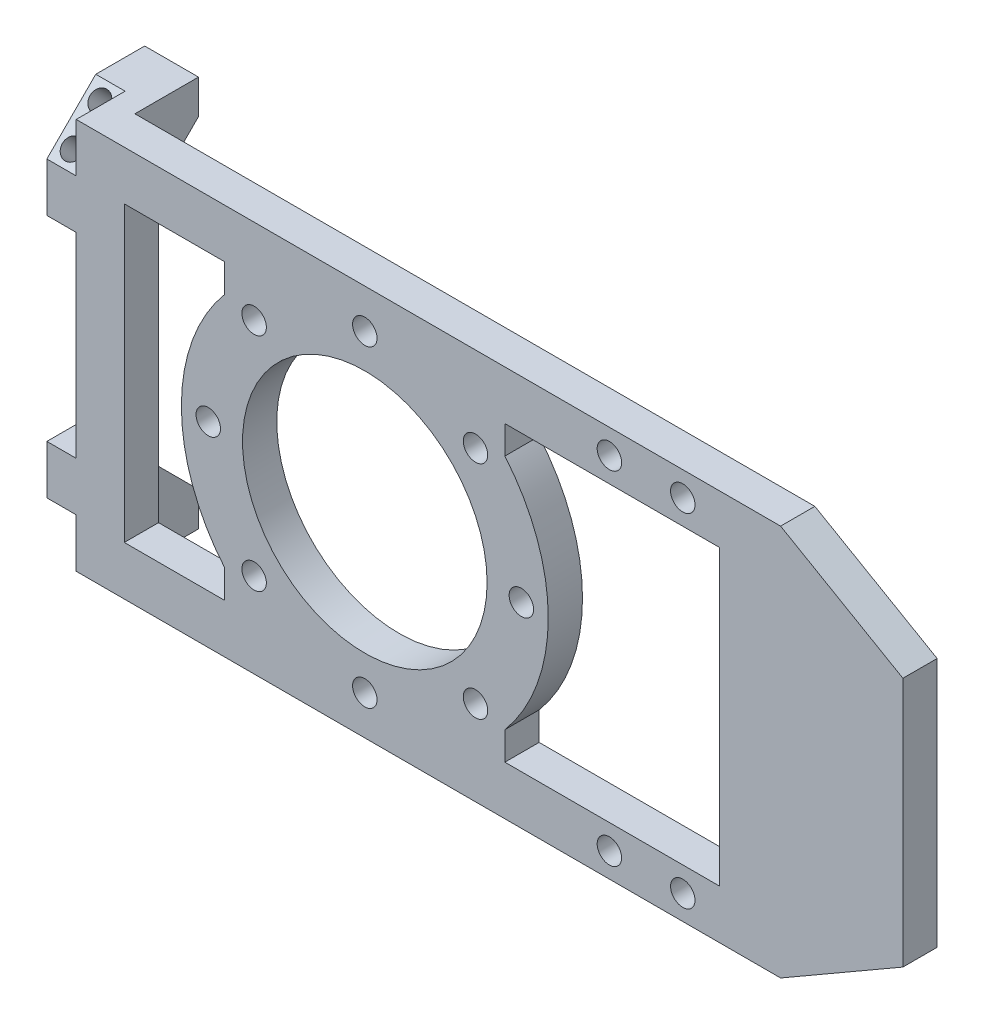
SolidWorks part; units mm, degrees
ref_plane "Front Plane" through (0, 0, 0) normal (0, 0, 1) x (1, 0, 0)
ref_plane "Top Plane" through (0, 0, 0) normal (0, 1, 0) x (1, 0, 0)
ref_plane "Right Plane" through (0, 0, 0) normal (1, 0, 0) x (0, 0, -1)
sketch "Sketch1" plane through (0, 0, 0) normal (0, 0, 1) x (1, 0, 0)
  line L1 (0, 0) -> (150, 0)
  line L2 (0, 0) -> (0, 80)
  line L3 (0, 80) -> (150, 80)
  line L4 (150, 0) -> (150, 80)
  dimension "D1" = 80
  dimension "D2" = 150
extrude "Boss-Extrude1" add sketch "Sketch1" along normal blind 7
sketch "Sketch2" plane through (0, 0, 7) normal (0, 0, 1) x (1, 0, 0)
  line L3 (0, 60) -> (6, 60)
  line L7 (0, 20) -> (6, 20)
  line L9 (0, 60) -> (6, 60)
  line L10 (0, 60) -> (0, 20)
  line L11 (0, 20) -> (6, 20)
  line L12 (6, 60) -> (6, 20)
  line M4 (0, 80) -> (0, 0)
extrude "Cut-Extrude2" cut sketch "Sketch2" against normal blind 7 contours L12 L3 L7 M4
sketch "Sketch3" plane through (0, 0, 7) normal (0, 0, 1) x (1, 0, 0)
  line L0 (150, 0) -> (150, 80) construction
  circle A0 centre (65, 40) radius 25
  dimension "D1" = 50
  dimension "D2" = 85
extrude "Cut-Extrude3" cut sketch "Sketch3" against normal blind 7
sketch "Sketch4" plane through (0, 0, 7) normal (0, 0, 1) x (1, 0, 0)
  line L0 (15.8284, 69.9752) -> (15.8284, 10.0248)
  line L1 (15.8284, 69.9752) -> (36.3588, 69.9752)
  line L3 (15.8284, 10.0248) -> (36.3588, 10.0248)
  line L5 (-2.1302, 69.9752) -> (42.4669, 10.0248) construction
  line L6 (-2.1302, 10.0248) -> (42.4669, 69.9752) construction
  line L7 (36.3588, 69.9752) -> (36.3588, 64.206)
  line L8 (36.3588, 15.794) -> (36.3588, 10.0248)
  arc A0 (36.3588, 64.206) -> (36.3588, 15.794) centre (65, 40) ccw
  point P3 (20.1684, 40)
  dimension "D1" = 75
extrude "Cut-Extrude5" cut sketch "Sketch4" against normal blind 7
sketch "Sketch5" plane through (0, 0, 7) normal (0, 0, 1) x (1, 0, 0)
  line L0 (93.6312, 69.9752) -> (93.6312, 64.2179)
  line L1 (93.6312, 69.9752) -> (137.5331, 69.9752)
  line L3 (93.6312, 10.0248) -> (137.5331, 10.0248)
  line L4 (137.5331, 69.9752) -> (137.5331, 10.0248)
  line L5 (93.6312, 15.7821) -> (93.6312, 10.0248)
  arc A0 (93.6312, 15.7821) -> (93.6312, 64.2179) centre (65, 40) ccw
extrude "Cut-Extrude6" cut sketch "Sketch5" against normal blind 7
sketch "Sketch6" plane through (0, 0, 7) normal (0, 0, 1) x (1, 0, 0)
  circle A0 centre (97, 40) radius 2.5
  circle A1 centre (65, 40) radius 25 construction
  circle A2 centre (87.6274, 17.3726) radius 2.5
  circle A3 centre (65, 8) radius 2.5
  circle A4 centre (42.3726, 17.3726) radius 2.5
  circle A5 centre (33, 40) radius 2.5
  circle A6 centre (42.3726, 62.6274) radius 2.5
  circle A7 centre (65, 72) radius 2.5
  circle A8 centre (87.6274, 62.6274) radius 2.5
  point P20 (65, 40)
  dimension "D1" = 5
  dimension "D2" = 32
  dimension "D3" = 8
extrude "Cut-Extrude7" cut sketch "Sketch6" against normal blind 7
sketch "Sketch8" plane through (0, 0, 0) normal (-1, 0, 0) x (0, 0, 1)
  line L0 (0, 60) -> (-20, 80)
  line L1 (-20, 80) -> (0, 80)
  line L2 (0, 80) -> (0, 60)
extrude "Boss-Extrude2" add sketch "Sketch8" against normal blind 6
sketch "Sketch9" plane through (0, 0, 0) normal (-1, 0, 0) x (0, 0, 1)
  line L0 (-13, 80) -> (-13, 73)
  line L1 (7, 80) -> (-20, 80) construction
  line L2 (-20, 80) -> (0, 60) construction
  line L3 (0, 60) -> (0, 20) construction
  line L4 (-13, 73) -> (-20, 80)
  line L5 (-20, 80) -> (-13, 80)
  dimension "D1" = 13
extrude "Cut-Extrude8" cut sketch "Sketch9" against normal blind 6
sketch "Sketch10" plane through (0, 0, 0) normal (0, 0, -1) x (-1, 0, 0)
  line L1 (-6, 20) -> (0, 20)
  line L2 (-6, 20) -> (-6, 0)
  line L3 (-6, 0) -> (0, 0)
  line L4 (0, 20) -> (0, 0)
extrude "Boss-Extrude3" add sketch "Sketch10" along normal blind 13
sketch "Sketch11" plane through (0, 0, 0) normal (-1, 0, 0) x (0, 0, 1)
  line L0 (0, 20) -> (-13, 7)
  line L1 (-13, 0) -> (-13, 20) construction
  line L2 (-13, 7) -> (-13, 20)
  line L3 (-13, 20) -> (0, 20)
extrude "Cut-Extrude9" cut sketch "Sketch11" against normal blind 13
sketch "Sketch12" plane through (0, 0, 7) normal (0, 0, 1) x (1, 0, 0)
  line L0 (150, 0) -> (150, 80) construction
  line L1 (150, 80) -> (0, 80) construction
  line L3 (150, 40) -> (139.1151, 40) construction
  circle A0 centre (130, 75) radius 2.5
  circle A1 centre (115, 75) radius 2.5
  circle A2 centre (130, 5) radius 2.5
  circle A3 centre (115, 5) radius 2.5
  dimension "D1" = 20
  dimension "D2" = 5
  dimension "D3" = 5
  dimension "D4" = 5
  dimension "D5" = 15
extrude "Cut-Extrude10" cut sketch "Sketch12" against normal blind 13
sketch "Sketch13" plane through (6, 0, 0) normal (1, 0, 0) x (0, 0, -1)
  line L0 (0, 60) -> (13, 73)
  line L1 (13, 73) -> (13, 80)
  line L2 (13, 80) -> (0, 80)
  line L3 (0, 80) -> (0, 60)
  line L4 (-7, 40) -> (-3.6324, 40) construction
  line L5 (-7, 0) -> (-7, 80) construction
  line L6 (13, 0) -> (0, 0)
  line L7 (13, 7) -> (13, 0)
  line L8 (0, 20) -> (13, 7)
  line L9 (0, 0) -> (0, 20)
extrude "Boss-Extrude5" add sketch "Sketch13" along normal blind 5
sketch "Sketch14" plane through (0, 30, 30) normal (0, -0.7071, -0.7071) x (1, 0, 0)
  line L0 (3, -55.6188) -> (3, -47.6188)
  circle A0 centre (3, -47.6188) radius 2
  circle A1 centre (3, -55.6188) radius 2
  point P3 (3, -51.6188)
  point P5 (0, 0)
  dimension "D2" = 4
  dimension "D3" = 4
  dimension "D1" = 8
extrude "Cut-Extrude11" cut sketch "Sketch14" against normal through all
sketch "Sketch15" plane through (0, 0, 0) normal (-1, 0, 0) x (0, 0, 1)
  line L0 (7, 70) -> (-3, 80)
  line L1 (7, 80) -> (7, 60) construction
  line L2 (7, 80) -> (-13, 80) construction
  line L3 (-3, 80) -> (7, 80)
  line L4 (7, 80) -> (7, 70)
  line L5 (7, 40) -> (1.0916, 40) construction
  line L6 (7, 69.9752) -> (7, 10.0248) construction
  line L7 (-3, 0) -> (7, 0)
  line L8 (7, 10) -> (-3, 0)
  line L9 (7, 0) -> (7, 10)
extrude "Cut-Extrude13" cut sketch "Sketch15" against normal blind 6
sketch "Sketch16" plane through (6, 0, 0) normal (-1, 0, 0) x (0, 0, 1)
  line L0 (7, 40) -> (1.9924, 40) construction
  line L1 (7, 60) -> (7, 20) construction
ref_plane "Plane2" through (0, 40, 0) normal (0, -1, 0) x (0, 0, -1)
mirror "Mirror1" about plane through (0, 40, 0) normal (0, -1, 0) of "Cut-Extrude11"
sketch "Sketch17" plane through (0, 0, 7) normal (0, 0, 1) x (1, 0, 0)
  line L0 (150, 80) -> (175, 65.5662)
  line L1 (175, 65.5662) -> (175, 14.4338)
  line L2 (175, 14.4338) -> (150, 0)
  line L3 (150, 0) -> (150, 80) construction
  line L4 (150, 80) -> (150, 0)
  dimension "D1" = 60
  dimension "D2" = 60
  dimension "D3" = 25
extrude "Boss-Extrude6" add sketch "Sketch17" against normal blind 7
